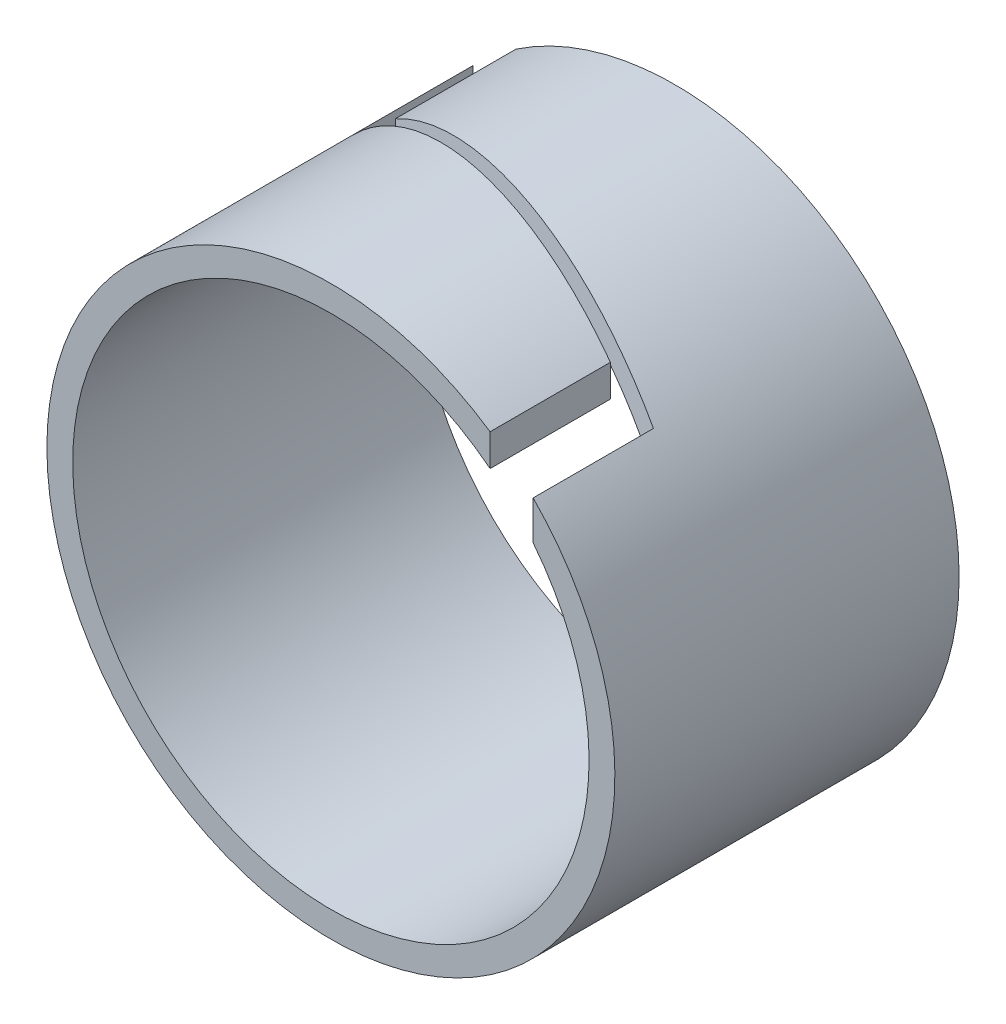
SolidWorks part; units mm, degrees
material "Zinc AC41A Alloy, As Cast"
ref_plane "Front Plane" through (0, 0, 0) normal (0, 0, 1) x (1, 0, 0)
ref_plane "Top Plane" through (0, 0, 0) normal (0, 1, 0) x (1, 0, 0)
ref_plane "Right Plane" through (0, 0, 0) normal (1, 0, 0) x (0, 0, -1)
sketch "Sketch2" plane through (0, 0, 0) normal (0, 0, 1) x (1, 0, 0)
  circle A0 centre (0, 0) radius 3.3
  circle A1 centre (0, 0) radius 3
  dimension "D1" = 6
  dimension "D2" = 6.6
extrude "Boss-Extrude1" add sketch "Sketch2" along normal blind 4
ref_plane "Plane1" through (0, 3.3, 0) normal (0, 1, 0) x (1, 0, 0)
sketch "Sketch3" plane through (0, 3.3, 0) normal (0, 1, 0) x (1, 0, 0)
  line L0 (1.85, -4) -> (2.35, -4)
  line L2 (-2.35, 0) -> (-1.85, 0)
  line L3 (0, 0) -> (0, -4)
  line L4 (-1.85, 0) -> (-1.85, -5.3179) construction
  line L5 (-2.35, 0) -> (-2.35, -1.4) construction
  line L6 (-1.85, 0) -> (-1.85, -1.4) construction
  line L7 (0, 0) -> (0, -4) construction
  line L8 (-3.3, 0) -> (3.3, 0)
  line L9 (-3.3, 0) -> (3.3, 0) construction
  line L10 (2.35, -4) -> (2.35, -2.6018)
  line L12 (-1.85, 0) -> (-1.85, -1.4)
  line L13 (1.85, -4) -> (1.85, -2.6018)
  line L15 (-2.35, -1.4) -> (-2.35, 0)
  line L16 (3.3, 0) -> (3.3, -4)
  line L17 (0, -5) -> (0, -50000) construction
  line L18 (3.3, 0) -> (3.3, -4) construction
  line L19 (3.3, -4) -> (-3.3, -4)
  line L20 (3.3, -4) -> (-3.3, -4) construction
  line L21 (-3.3, -4) -> (-3.3, 0)
  line L22 (-3.3, -4) -> (-3.3, 0) construction
  line L23 (-2.35, -1.4) -> (1.85, -2.6018)
  line L24 (2.35, -2.6018) -> (-1.85, -1.4)
  point P11 (0, 0)
  point P20 (0, -5)
  dimension "D1" = 2.35
  dimension "D2" = 0.5
  dimension "D3" = 1.4
  dimension "D4" = 0.5
  dimension "D5" = 2.35
extrude "Cut-Extrude1" cut sketch "Sketch3" against normal blind 5
